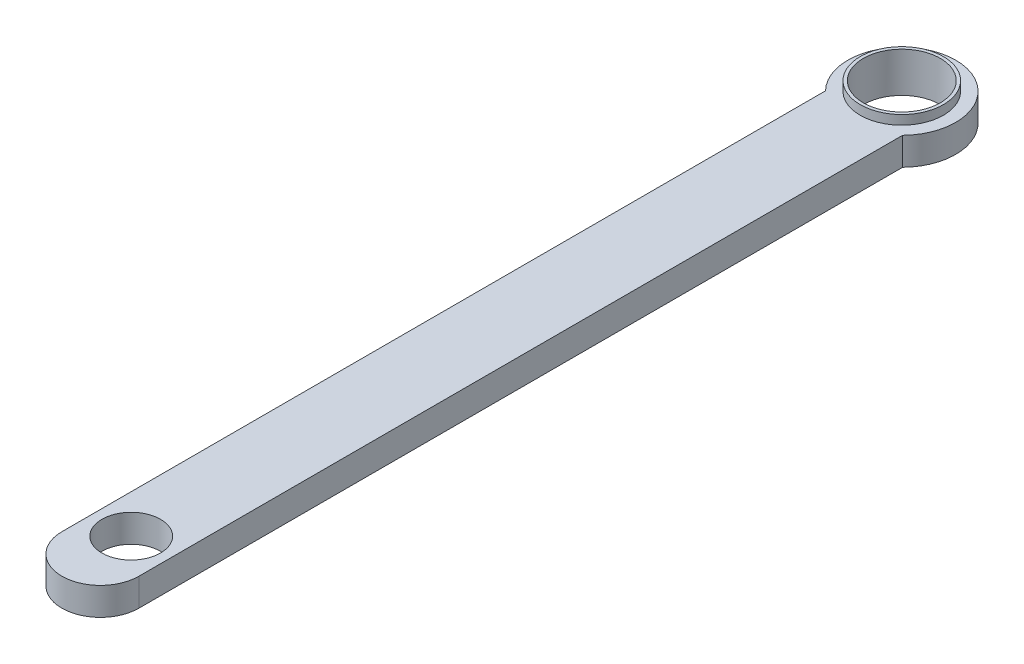
SolidWorks part; units mm, degrees
material "7075-T6 (SN)"
ref_plane "정면" through (0, 0, 0) normal (0, 0, 1) x (1, 0, 0)
ref_plane "윗면" through (0, 0, 0) normal (0, 1, 0) x (1, 0, 0)
ref_plane "우측면" through (0, 0, 0) normal (1, 0, 0) x (0, 0, -1)
sketch "스케치1" plane through (0, 0, 0) normal (0, 1, 0) x (1, 0, 0)
  line L0 (-12.5, -260) -> (-12.5, -12.2474)
  line L1 (0, 0) -> (0, -260) construction
  line L2 (12.5, -260) -> (12.5, -12.2474)
  arc A1 (12.5, -12.2474) -> (-12.5, -12.2474) centre (0, 0) ccw
  arc A2 (-12.5, -260) -> (12.5, -260) centre (0, -260) ccw
  dimension "D2" = 35
  dimension "D3" = 25
  dimension "D4" = 260
extrude "보스-돌출1" add sketch "스케치1" along normal blind 9
sketch "스케치2" plane through (0, 9, 0) normal (0, 1, 0) x (1, 0, 0)
  circle A0 centre (0, 0) radius 12.5
  arc A1 (12.5, -12.2474) -> (-12.5, -12.2474) centre (0, 0) ccw construction
  dimension "D1" = 25
extrude "컷-돌출1" cut sketch "스케치2" against normal through all
sketch "스케치3" plane through (0, 9, 0) normal (0, 1, 0) x (1, 0, 0)
  circle A0 centre (0, 0) radius 13.5
  circle A1 centre (0, 0) radius 12.5 construction
  circle A2 centre (0, 0) radius 12.5
  dimension "D1" = 27
extrude "보스-돌출2" add sketch "스케치3" along normal blind 3
sketch "스케치4" plane through (0, 0, 0) normal (0, -1, 0) x (1, 0, 0)
  circle A0 centre (0, 0) radius 13.5
  circle A1 centre (0, 0) radius 12.5 construction
  circle A2 centre (0, 0) radius 12.5
  dimension "D1" = 27
extrude "보스-돌출3" add sketch "스케치4" along normal blind 1
sketch "스케치5" plane through (0, 9, 0) normal (0, 1, 0) x (1, 0, 0)
  circle A0 centre (0, -250) radius 9.5
  dimension "D1" = 19
  dimension "D2" = 250
extrude "컷-돌출2" cut sketch "스케치5" against normal through all
